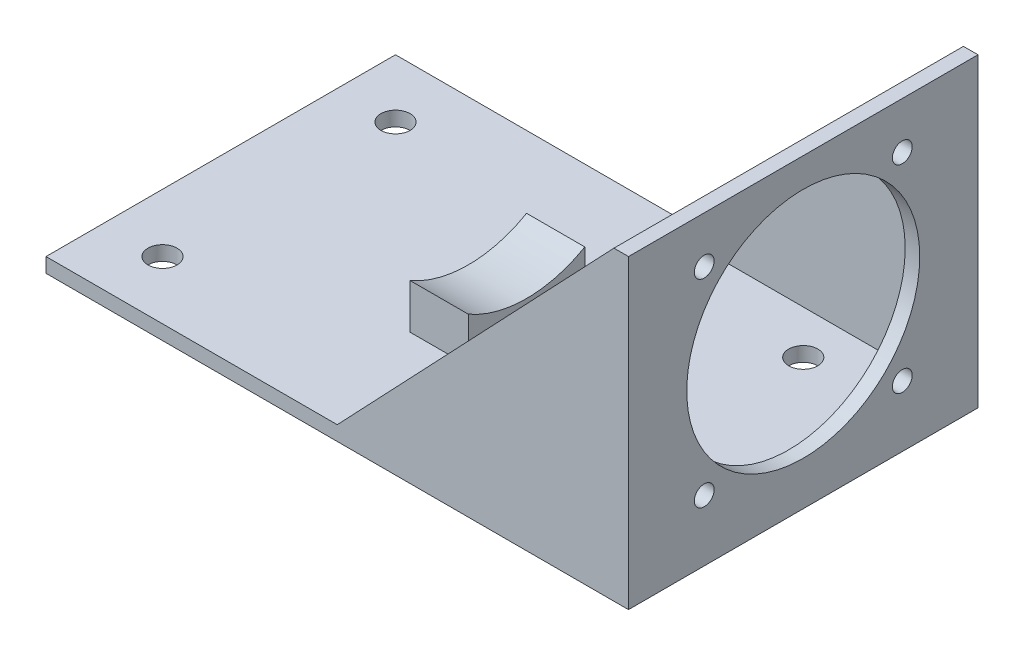
SolidWorks part; units mm, degrees
material "Cast Carbon Steel"
ref_plane "Front Plane" through (0, 0, 0) normal (0, 0, 1) x (1, 0, 0)
ref_plane "Top Plane" through (0, 0, 0) normal (0, 1, 0) x (1, 0, 0)
ref_plane "Right Plane" through (0, 0, 0) normal (1, 0, 0) x (0, 0, -1)
sketch "Sketch1" plane through (0, 0, 0) normal (0, 1, 0) x (1, 0, 0)
  line L1 (-127, 76.2) -> (127, 76.2)
  line L2 (-127, 76.2) -> (-127, -76.2)
  line L3 (-127, -76.2) -> (127, -76.2)
  line L4 (127, 76.2) -> (127, -76.2)
  line L5 (-127, 76.2) -> (127, -76.2) construction
  line L6 (-127, -76.2) -> (127, 76.2) construction
  point P0 (0, 0)
  dimension "D1" = 254
  dimension "D2" = 152.4
extrude "Boss-Extrude1" add sketch "Sketch1" along normal blind 6.35
sketch "Sketch2" plane through (127, 0, 0) normal (1, 0, 0) x (0, 0, -1)
  line L1 (-76.2, 6.35) -> (76.2, 6.35)
  line L2 (-76.2, 6.35) -> (-76.2, 133.35)
  line L3 (-76.2, 133.35) -> (76.2, 133.35)
  line L4 (76.2, 6.35) -> (76.2, 133.35)
  circle A0 centre (0, 69.85) radius 50.8
  circle A1 centre (-43.18, 26.67) radius 4.318
  circle A2 centre (43.18, 26.67) radius 4.318
  circle A3 centre (43.18, 113.03) radius 4.318
  circle A4 centre (-43.18, 113.03) radius 4.318
  dimension "D5" = 101.6
  dimension "D7" = 8.636
  dimension "D10" = 8.636
  dimension "D12" = 8.636
  dimension "D14" = 8.636
  dimension "D1" = 127
  dimension "D2" = 152.4
  dimension "D3" = 76.2
  dimension "D4" = 63.5
  dimension "D6" = 43.18
  dimension "D8" = 43.18
  dimension "D9" = 43.18
  dimension "D11" = 43.18
  dimension "D13" = 43.18
  dimension "D15" = 43.18
  dimension "D16" = 43.18
  dimension "D17" = 43.18
extrude "Boss-Extrude2" add sketch "Sketch2" against normal blind 6.35
sketch "Sketch3" plane through (0, 0, 76.2) normal (0, 0, 1) x (1, 0, 0)
  line L0 (120.65, 133.35) -> (0, 6.35)
  line L1 (-127, 6.35) -> (120.65, 6.35) construction
  line L2 (0, 6.35) -> (120.65, 6.35)
  line L3 (120.65, 6.35) -> (120.65, 133.35)
extrude "Boss-Extrude3" add sketch "Sketch3" against normal blind 6.35
sketch "Sketch4" plane through (0, 0, -76.2) normal (0, 0, -1) x (-1, 0, 0)
  line L0 (-120.65, 133.35) -> (0, 6.35)
  line L1 (0, 6.35) -> (-120.65, 6.35)
  line L2 (-120.65, 6.35) -> (-120.65, 133.35)
extrude "Boss-Extrude4" add sketch "Sketch4" against normal blind 6.35
sketch "Sketch5" plane through (0, 6.35, 0) normal (0, 1, 0) x (1, 0, 0)
  line L0 (120.65, -69.85) -> (120.65, 69.85) construction
  line L1 (-19.05, 25.4) -> (6.35, 25.4)
  line L2 (-19.05, 25.4) -> (-19.05, -25.4)
  line L3 (-19.05, -25.4) -> (6.35, -25.4)
  line L4 (6.35, 25.4) -> (6.35, -25.4)
  line L5 (-19.05, 25.4) -> (6.35, -25.4) construction
  line L6 (-19.05, -25.4) -> (6.35, 25.4) construction
  line L7 (0, 76.2) -> (-127, 76.2) construction
  point P0 (-6.35, 0)
  dimension "D1" = 127
  dimension "D2" = 76.2
  dimension "D3" = 50.8
  dimension "D4" = 25.4
extrude "Boss-Extrude5" add sketch "Sketch5" along normal blind 25.4
sketch "Sketch6" plane through (-19.05, 0, 0) normal (-1, 0, 0) x (0, 0, 1)
  line L0 (-76.2, 0) -> (76.2, 0) construction
  circle A0 centre (0, 69.85) radius 50.8
  dimension "D2" = 101.6
  dimension "D1" = 69.85
  dimension "D3" = 76.2
extrude "Cut-Extrude1" cut sketch "Sketch6" against normal blind 25.4
sketch "Sketch7" plane through (0, 6.35, 0) normal (0, 1, 0) x (1, 0, 0)
  line L0 (0, 76.2) -> (-127, 76.2) construction
  line L1 (127, 76.2) -> (127, -76.2) construction
  circle A0 centre (-101.6, 50.8) radius 6.35
  circle A1 centre (-101.6, -50.8) radius 6.35
  circle A2 centre (76.2, -50.8) radius 6.35
  circle A3 centre (76.2, 50.8) radius 6.35
  dimension "D3" = 12.7
  dimension "D4" = 12.7
  dimension "D5" = 12.7
  dimension "D6" = 12.7
  dimension "D1" = 25.4
  dimension "D2" = 25.4
  dimension "D7" = 101.6
  dimension "D8" = 50.8
extrude "Cut-Extrude2" cut sketch "Sketch7" against normal blind 25.4
